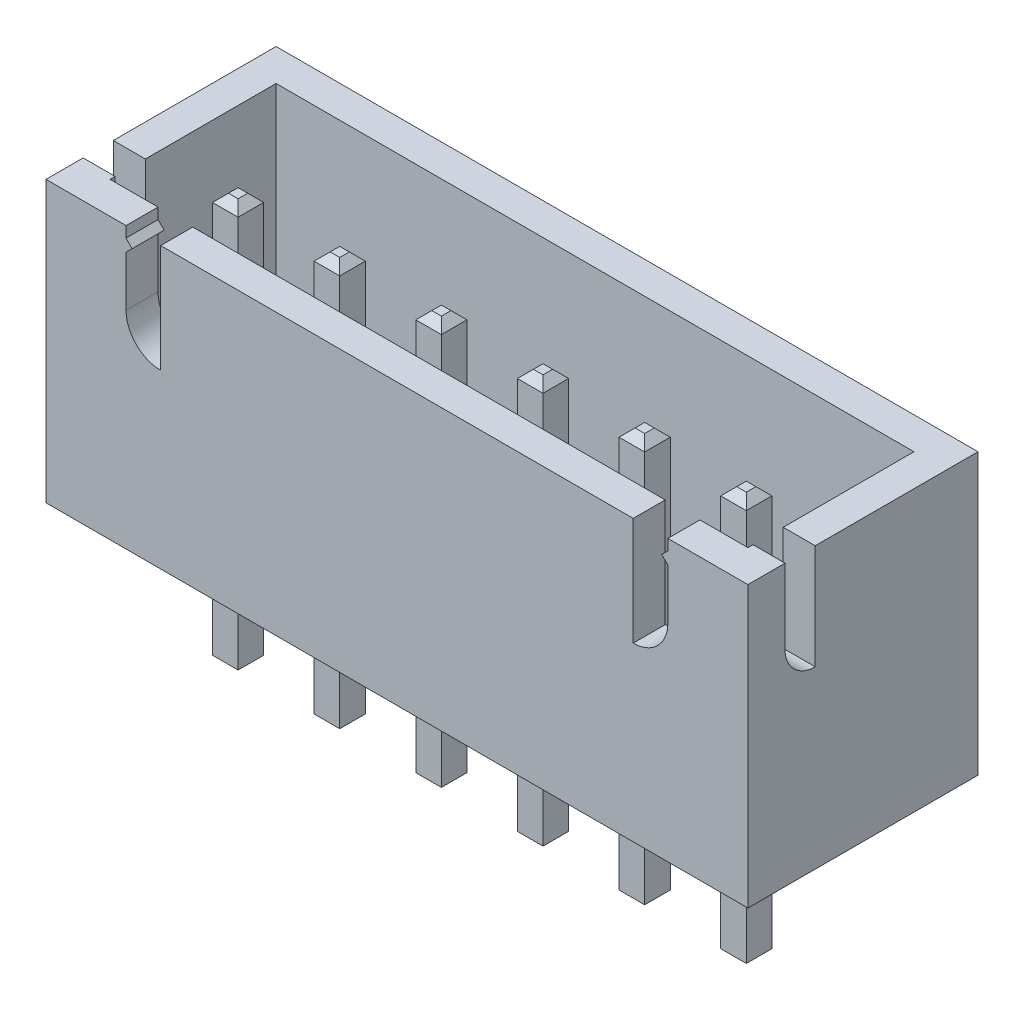
SolidWorks part; units mm, degrees
other "Camera1"
ref_plane "Front Plane" through (0, 0, 0) normal (0, 0, 1) x (1, 0, 0)
ref_plane "Top Plane" through (0, 0, 0) normal (0, 1, 0) x (1, 0, 0)
ref_plane "Right Plane" through (0, 0, 0) normal (1, 0, 0) x (0, 0, -1)
sketch "Sketch1" plane through (0, 0, 0) normal (0, 1, 0) x (1, 0, 0)
  line L1 (-8.77, 2.875) -> (8.77, 2.875)
  line L2 (-8.77, 2.875) -> (-8.77, -2.875)
  line L3 (-8.77, -2.875) -> (8.77, -2.875)
  line L4 (8.77, 2.875) -> (8.77, -2.875)
  line L5 (-8.77, 2.875) -> (8.77, -2.875) construction
  line L6 (-8.77, -2.875) -> (8.77, 2.875) construction
  point P0 (0, 0)
  dimension "D1" = 5.75
  dimension "D2" = 17.54
extrude "Boss-Extrude1" add sketch "Sketch1" along normal blind 7
shell "Shell1" thickness 0.8
sketch "Sketch2" plane through (8.77, 0, 0) normal (1, 0, 0) x (0, 0, -1)
  line L0 (-1.193, 7) -> (-1.193, 4.3796)
  line L1 (-2.875, 7) -> (2.875, 7) construction
  line L2 (-1.9469, 5.1335) -> (-1.9469, 7)
  line L3 (-1.9469, 7) -> (-1.193, 7)
  arc A0 (-1.193, 4.3796) -> (-1.9469, 5.1335) centre (-1.193, 5.1335) cw
extrude "Cut-Extrude1" cut sketch "Sketch2" against normal through all
sketch "Sketch3" plane through (0, 0, 2.875) normal (0, 0, 1) x (1, 0, 0)
  line L0 (-6.77, 7) -> (-6.77, 6.7289)
  line L1 (-8.77, 7) -> (8.77, 7) construction
  line L2 (-6.77, 6.7289) -> (-6.6171, 6.5761)
  line L3 (-6.6171, 6.5761) -> (-6.77, 6.4232)
  line L4 (-6.77, 6.4232) -> (-6.77, 5.1663)
  line L5 (-5.9038, 4.3001) -> (-5.9038, 7)
  line L6 (-5.9038, 7) -> (-6.77, 7)
  line L7 (-8.77, 7) -> (-8.77, 0) construction
  line L8 (0, 7) -> (0, 0) construction
  line L9 (5.9038, 7) -> (6.77, 7)
  line L10 (5.9038, 4.3001) -> (5.9038, 7)
  line L11 (6.77, 6.4232) -> (6.77, 5.1663)
  line L12 (6.6171, 6.5761) -> (6.77, 6.4232)
  line L13 (6.77, 6.7289) -> (6.6171, 6.5761)
  line L14 (6.77, 7) -> (6.77, 6.7289)
  arc A0 (-6.77, 5.1663) -> (-5.9038, 4.3001) centre (-5.9038, 5.1663) ccw
  arc A1 (6.77, 5.1663) -> (5.9038, 4.3001) centre (5.9038, 5.1663) cw
  dimension "D1" = 2
extrude "Cut-Extrude2" cut sketch "Sketch3" against normal up to next
sketch "Sketch4" plane through (0, 0, 0) normal (0, -1, 0) x (1, 0, 0)
  line L0 (-8.77, -2.875) -> (-8.77, 2.875) construction
  line L1 (-6.64, 0.845) -> (-6, 0.845)
  line L2 (-6.64, 0.845) -> (-6.64, 0.205)
  line L3 (-6.64, 0.205) -> (-6, 0.205)
  line L4 (-6, 0.845) -> (-6, 0.205)
  line L5 (-6.64, 0.845) -> (-6, 0.205) construction
  line L6 (-6.64, 0.205) -> (-6, 0.845) construction
  line L9 (-8.77, 2.875) -> (8.77, 2.875) construction
  line L10 (-4.1, 0.845) -> (-3.46, 0.845)
  line L11 (-3.46, 0.845) -> (-3.46, 0.205)
  line L12 (-4.1, 0.205) -> (-3.46, 0.205)
  line L13 (-4.1, 0.845) -> (-4.1, 0.205)
  line L14 (-1.56, 0.845) -> (-0.92, 0.845)
  line L15 (-0.92, 0.845) -> (-0.92, 0.205)
  line L16 (-1.56, 0.205) -> (-0.92, 0.205)
  line L17 (-1.56, 0.845) -> (-1.56, 0.205)
  line L18 (0.98, 0.845) -> (1.62, 0.845)
  line L19 (1.62, 0.845) -> (1.62, 0.205)
  line L20 (0.98, 0.205) -> (1.62, 0.205)
  line L21 (0.98, 0.845) -> (0.98, 0.205)
  line L22 (3.52, 0.845) -> (4.16, 0.845)
  line L23 (4.16, 0.845) -> (4.16, 0.205)
  line L24 (3.52, 0.205) -> (4.16, 0.205)
  line L25 (3.52, 0.845) -> (3.52, 0.205)
  line L26 (6.06, 0.845) -> (6.7, 0.845)
  line L27 (6.7, 0.845) -> (6.7, 0.205)
  line L28 (6.06, 0.205) -> (6.7, 0.205)
  line L29 (6.06, 0.845) -> (6.06, 0.205)
  point P0 (-6.32, 0.525)
  dimension "D1" = 0.64
  dimension "D2" = 0.64
  dimension "D3" = 2.45
  dimension "D4" = 2.35
  dimension "D5" = 6
extrude "Boss-Extrude2" add sketch "Sketch4" along normal blind 3.45 and the other way blind 6.75
chamfer "Chamfer1" distance 0.2 angle 45 48 edges at (6.06, -3.45, 0.525) (6.38, -3.45, 0.845) (6.7, -3.45, 0.525) (6.38, -3.45, 0.205) (3.52, -3.45, 0.525) (3.84, -3.45, 0.845) (4.16, -3.45, 0.525) (3.84, -3.45, 0.205) (0.98, -3.45, 0.525) (1.3, -3.45, 0.845) (1.62, -3.45, 0.525) (1.3, -3.45, 0.205) (-1.56, -3.45, 0.525) (-1.24, -3.45, 0.845) (-0.92, -3.45, 0.525) (-1.24, -3.45, 0.205) (-4.1, -3.45, 0.525) (-3.78, -3.45, 0.845) (-3.46, -3.45, 0.525) (-3.78, -3.45, 0.205) (-6.32, -3.45, 0.205) (-6.64, -3.45, 0.525) (-6.32, -3.45, 0.845) (-6, -3.45, 0.525) (6.7, 6.75, 0.525) (6.38, 6.75, 0.845) (6.06, 6.75, 0.525) (6.38, 6.75, 0.205) (4.16, 6.75, 0.525) (3.84, 6.75, 0.845) (3.52, 6.75, 0.525) (3.84, 6.75, 0.205) (1.62, 6.75, 0.525) (1.3, 6.75, 0.845) (0.98, 6.75, 0.525) (1.3, 6.75, 0.205) (-0.92, 6.75, 0.525) (-1.24, 6.75, 0.845) (-1.56, 6.75, 0.525) (-1.24, 6.75, 0.205) (-3.46, 6.75, 0.525) (-3.78, 6.75, 0.845) (-4.1, 6.75, 0.525) (-3.78, 6.75, 0.205) (-6.32, 6.75, 0.845) (-6.64, 6.75, 0.525) (-6.32, 6.75, 0.205) (-6, 6.75, 0.525)
